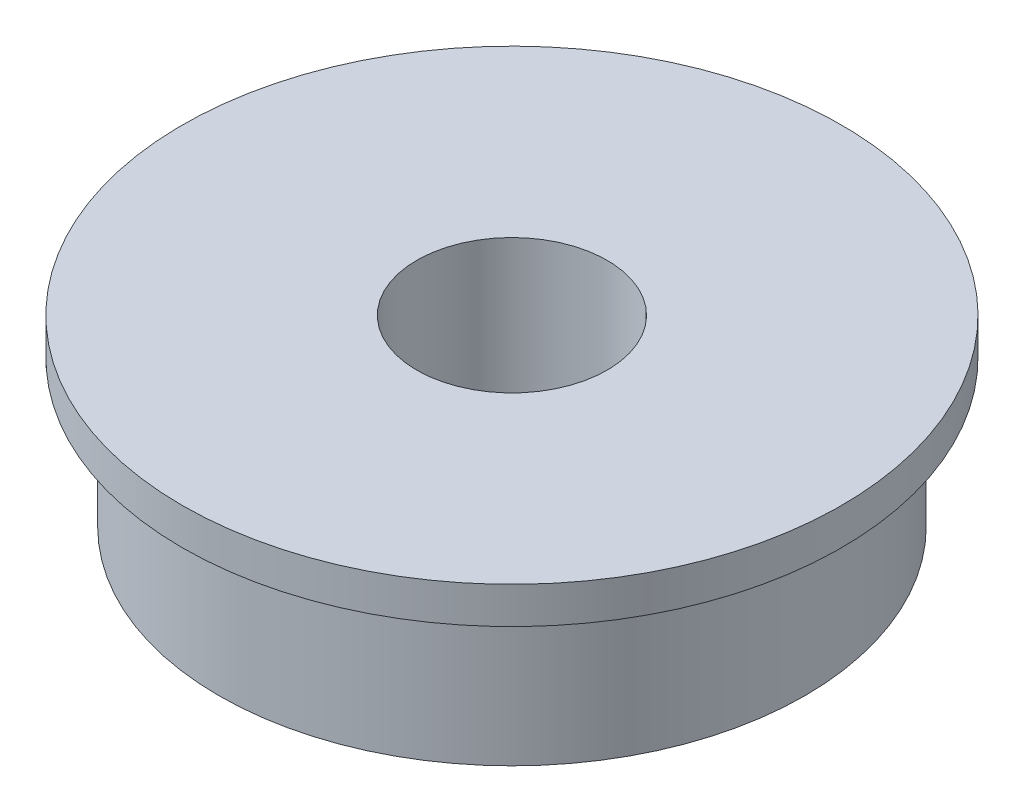
SolidWorks part; units mm, degrees
material "1023 碳钢板 (SS)"
ref_plane "前视基准面" through (0, 0, 0) normal (0, 0, 1) x (1, 0, 0)
ref_plane "上视基准面" through (0, 0, 0) normal (0, 1, 0) x (1, 0, 0)
ref_plane "右视基准面" through (0, 0, 0) normal (1, 0, 0) x (0, 0, -1)
sketch "草图1" plane through (0, 0, 0) normal (0, 1, 0) x (1, 0, 0)
  circle A0 centre (0, 0) radius 2.6
  circle A1 centre (0, 0) radius 8
  dimension "D1" = 5.2
  dimension "D2" = 16
extrude "凸台-拉伸1" add sketch "草图1" along normal blind 5
sketch "草图2" plane through (0, 5, 0) normal (0, 1, 0) x (1, 0, 0)
  circle A0 centre (0, 0) radius 2.6
  circle A1 centre (0, 0) radius 9
  circle A2 centre (0, 0) radius 2.6 construction
  dimension "D1" = 18
extrude "凸台-拉伸2" add sketch "草图2" against normal blind 1
